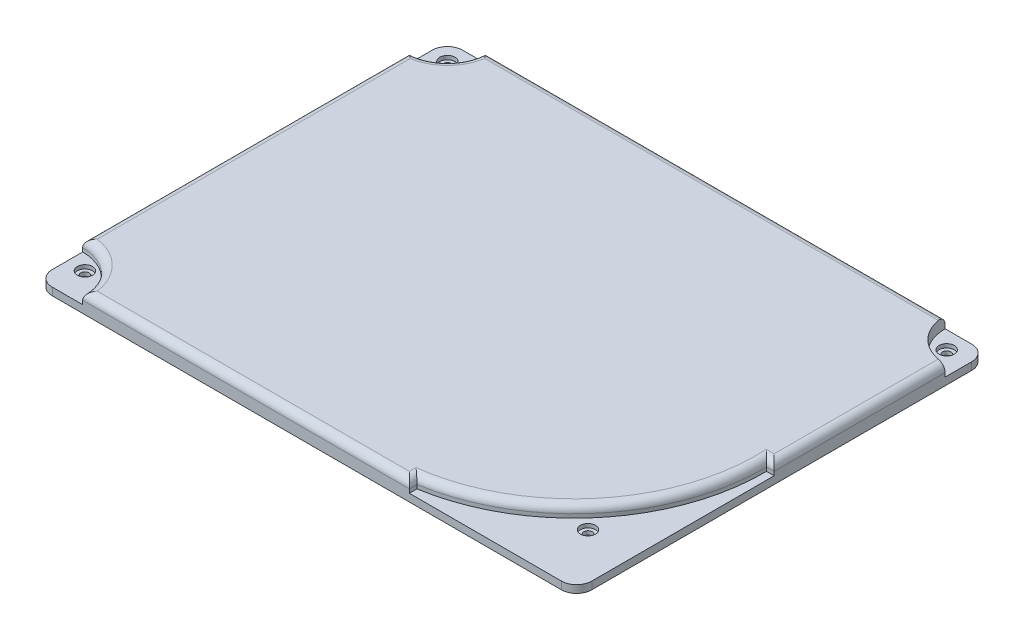
SolidWorks part; units mm, degrees
material "6061-T6 (SS)"
ref_plane "Front Plane" through (0, 0, 0) normal (0, 0, 1) x (1, 0, 0)
ref_plane "Top Plane" through (0, 0, 0) normal (0, 1, 0) x (1, 0, 0)
ref_plane "Right Plane" through (0, 0, 0) normal (1, 0, 0) x (0, 0, -1)
sketch "Sketch1" plane through (0, 0, 0) normal (0, 1, 0) x (1, 0, 0)
  line L1 (-35.5, -27) -> (35.5, -27)
  line L2 (-35.5, -27) -> (-35.5, 27)
  line L3 (-35.5, 27) -> (35.5, 27)
  line L4 (35.5, -27) -> (35.5, 27)
  line L5 (-35.5, -27) -> (35.5, 27) construction
  line L6 (-35.5, 27) -> (35.5, -27) construction
  point P0 (0, 0)
  dimension "D1" = 71
  dimension "D2" = 54
extrude "Boss-Extrude1" add sketch "Sketch1" along normal blind 2.5
hole_wizard "M1.4x0.3 Tapped Hole1" positions "Sketch2" profile "Sketch3" tap size "M1.4x0.3" standard "ANSI Metric" end condition through all
sketch "Sketch2" plane through (0, 2.5, 0) normal (0, 1, 0) x (1, 0, 0)
  line L0 (-35.5, 27) -> (-35.5, -27) construction
  line L1 (35.5, 27) -> (-35.5, 27) construction
  line L2 (-35.5, -27) -> (35.5, -27) construction
  line L3 (35.5, -27) -> (35.5, 27) construction
  point P0 (-33.2, 24.7)
  point P2 (32.5, 24.7)
  point P4 (-33.2, -23)
  point P6 (29.4, -19.4)
  dimension "D1" = 2.3
  dimension "D2" = 2.3
  dimension "D3" = 4
  dimension "D4" = 2.3
  dimension "D5" = 7.6
  dimension "D6" = 6.1
  dimension "D7" = 3
  dimension "D8" = 2.3
cosmetic thread "Hole Thread1" parameters "D2"=1.4
cosmetic thread "Hole Thread2" parameters "D2"=1.4
cosmetic thread "Hole Thread3" parameters "D2"=1.4
cosmetic thread "Hole Thread4" parameters "D2"=1.4
sketch "Sketch3" plane through (-33.2, 2.5, -24.7) normal (1, 0, 0) x (0, 0, 1)
  line L0 (0, 0) -> (0, 2.5)
  line L1 (0, 2.5) -> (0.55, 2.5)
  line L2 (0.55, 2.5) -> (0.55, 0.175)
  line L3 (0.55, 0.175) -> (0.725, 0)
  line L5 (0.725, 0) -> (0, 0)
  line L6 (-0.55, 0.175) -> (-0.725, 0) construction
  line L11 (0, -6.35) -> (0, 107.95) construction
  dimension "Thru Tap Drill Dia." = 1.1
  dimension "Thru Tap Drill Depth" = 2.5
  dimension "Near C'Sink Dia." = 1.45
  dimension "Near C'Sink Angle" = 90
sketch "Sketch4" plane through (0, 0, 0) normal (0, -1, 0) x (1, 0, 0)
  line L0 (-35.5, -27) -> (-35.5, 27) construction
  line L1 (35.5, -27) -> (-35.5, -27) construction
  line L2 (-7.7481, 19) -> (-33.5, 19)
  line L4 (-6.5, -20) -> (-33.5, -20)
  line L5 (-33.5, 19) -> (-33.5, -20)
  line L6 (-35.5, 27) -> (35.5, 27) construction
  arc A0 (-6.5, -20) -> (-7.7481, 19) centre (8.5, 0) ccw
  dimension "D2" = 50
  dimension "D1" = 44
  dimension "D3" = 2
  dimension "D4" = 7
  dimension "D5" = 8
extrude "Cut-Extrude1" cut sketch "Sketch4" against normal blind 1.8
sketch "Sketch5" plane through (0, 2.5, 0) normal (0, 1, 0) x (1, 0, 0)
  line L1 (34.5, -1) -> (35.5, -1)
  line L2 (35.5, -27) -> (35.5, 27) construction
  line L3 (35.5, -1) -> (35.5, -27)
  line L5 (-35.5, 27) -> (-35.5, -27) construction
  line L6 (13.5, -26) -> (13.5, -27)
  line L7 (13.5, -27) -> (35.5, -27)
  line L8 (35.5, -27) -> (35.5, 27) construction
  line L9 (-35.5, -27) -> (35.5, -27) construction
  circle A0 centre (-35.5, -27) radius 6
  circle A1 centre (-35.5, 27) radius 5
  circle A3 centre (35.5, 27) radius 5.5
  arc A4 (34.5, -1) -> (13.5, -26) centre (9.5021, -1.3217) cw
  dimension "D1" = 10
  dimension "D2" = 11
  dimension "D3" = 12
  dimension "D4" = 25
  dimension "D5" = 1
  dimension "D6" = 1
  dimension "D7" = 22
  dimension "D8" = 26
extrude "Cut-Extrude2" cut sketch "Sketch5" against normal blind 1.5
fillet "Fillet1" radius 2 4 edges at (-35.5, 0.5, -27) (35.5, 0.5, -27) (35.5, 0.5, 27) (-35.5, 0.5, 27)
fillet "Fillet2" radius 1 9 edges at (-31.2574, 2.5, 22.7574) (-8, 2.5, 27) (13.5, 2.5, 26.5) (35.5, 2.5, -10.25) (35, 2.5, 1) (28.6447, 2.5, 17.4015) (-35.5, 2.5, -0.5) (-31.9645, 2.5, -23.4645) (-0.25, 2.5, -27)
sketch "Sketch6" plane through (0, 1, 0) normal (0, 1, 0) x (1, 0, 0)
  circle A0 centre (-33.2, 24.7) radius 1
  circle A1 centre (32.5, 24.7) radius 1
  circle A2 centre (29.4, -19.4) radius 1
  circle A3 centre (-33.2, -23) radius 1
  dimension "D1" = 2
  dimension "D2" = 2
  dimension "D3" = 2
  dimension "D4" = 2
extrude "Cut-Extrude4" cut sketch "Sketch6" against normal blind 0.5
